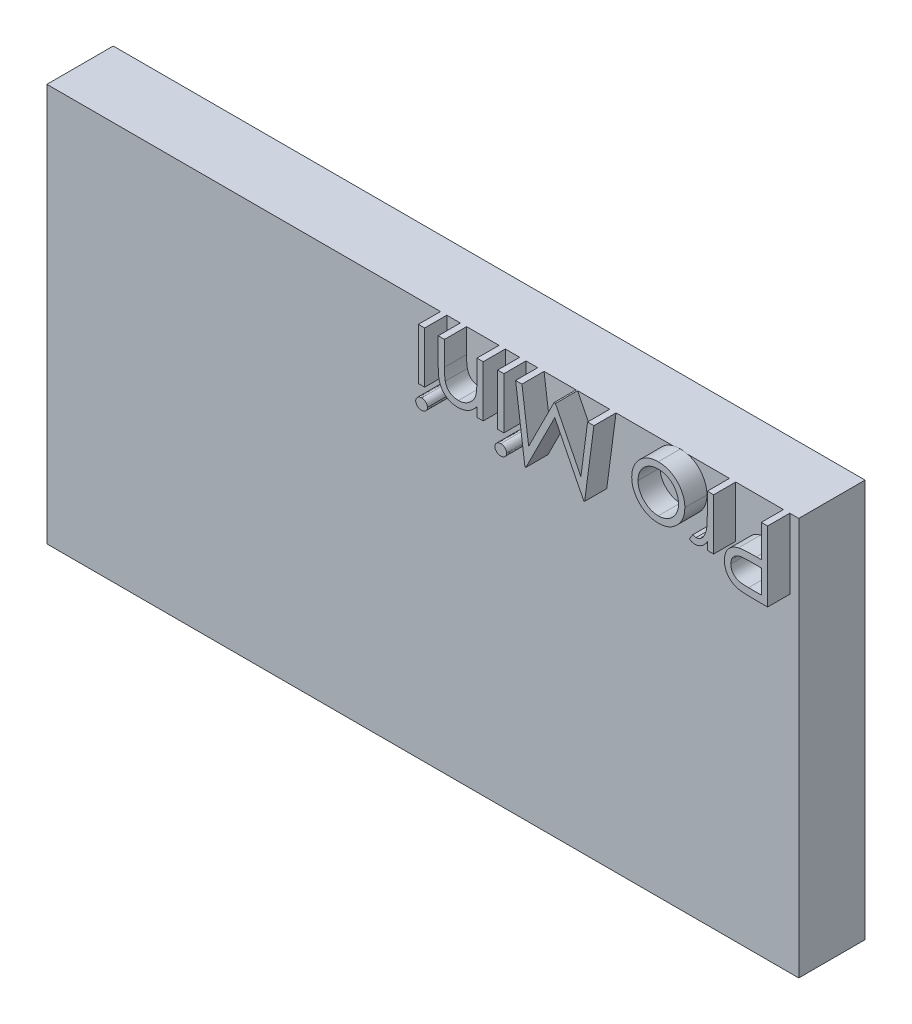
SolidWorks part; units mm, degrees
ref_plane "Front Plane" through (0, 0, 0) normal (0, 0, 1) x (1, 0, 0)
ref_plane "Top Plane" through (0, 0, 0) normal (0, 1, 0) x (1, 0, 0)
ref_plane "Right Plane" through (0, 0, 0) normal (1, 0, 0) x (0, 0, -1)
sketch "Sketch1" plane through (0, 0, 0) normal (0, 0, 1) x (1, 0, 0)
  line L4 (-34, 18) -> (0, 18)
  line L5 (-34, 18) -> (-34, 0)
  line L6 (-34, 0) -> (0, 0)
  line L7 (0, 18) -> (0, 0)
  point P5 (0, 9)
  dimension "D1" = 0
extrude "Boss-Extrude1" add sketch "Sketch1" along normal blind 3
sketch "Sketch2" plane through (0, 0, 3) normal (0, 0, 1) x (1, 0, 0)
  text T0 "Pro Mini\r\n"
extrude "Boss-Extrude2" add sketch "Sketch2" along normal blind 1
